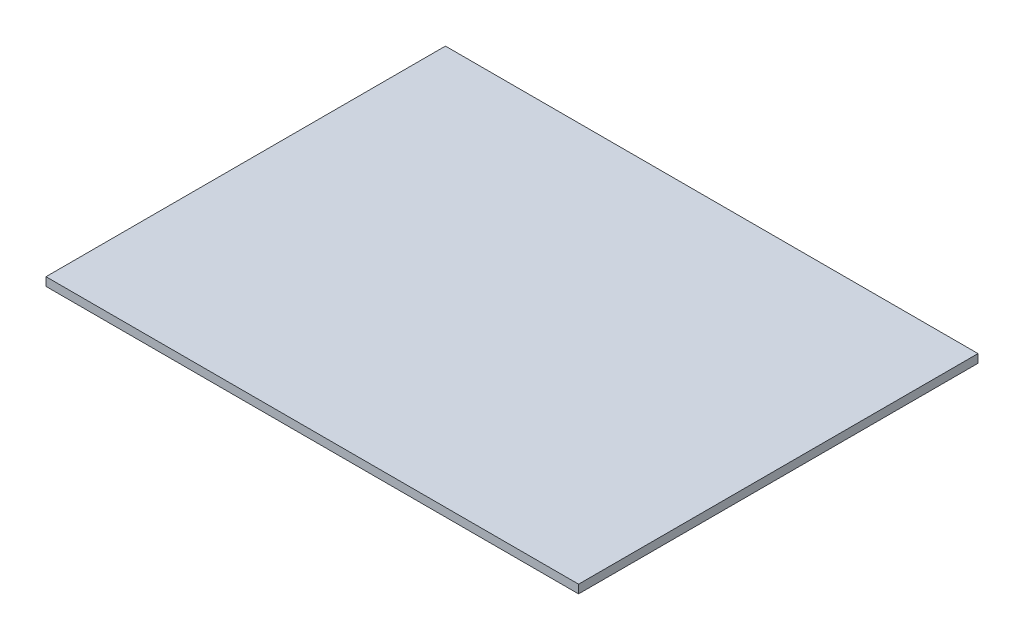
SolidWorks part; units mm, degrees
ref_plane "Front Plane" through (0, 0, 0) normal (0, 0, 1) x (1, 0, 0)
ref_plane "Top Plane" through (0, 0, 0) normal (0, 1, 0) x (1, 0, 0)
ref_plane "Right Plane" through (0, 0, 0) normal (1, 0, 0) x (0, 0, -1)
sketch "Sketch1" plane through (0, 0, 0) normal (0, 1, 0) x (1, 0, 0)
  line L1 (0, 0) -> (100, 0)
  line L2 (0, 0) -> (0, 75)
  line L3 (0, 75) -> (100, 75)
  line L4 (100, 0) -> (100, 75)
extrude "Boss-Extrude1" add sketch "Sketch1" along normal blind 1.5875
